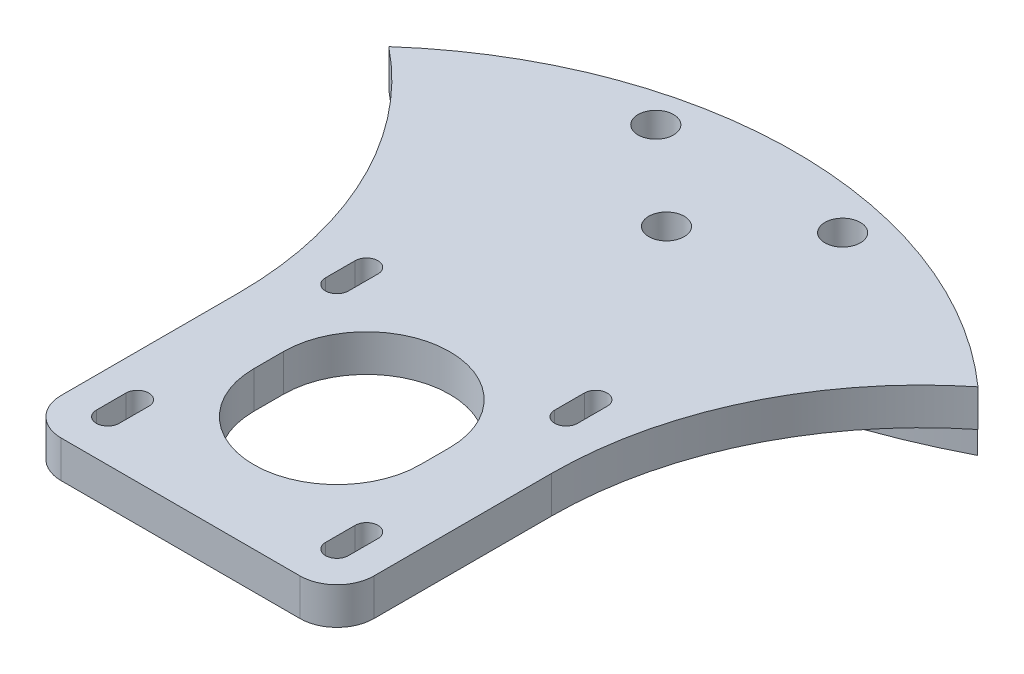
SolidWorks part; units mm, degrees
ref_plane "Front Plane" through (0, 0, 0) normal (0, 0, 1) x (1, 0, 0)
ref_plane "Top Plane" through (0, 0, 0) normal (0, 1, 0) x (1, 0, 0)
ref_plane "Right Plane" through (0, 0, 0) normal (1, 0, 0) x (0, 0, -1)
sketch "Sketch1" plane through (0, 0, 0) normal (0, 1, 0) x (1, 0, 0)
  circle A0 centre (0, 0) radius 72.63
  dimension "D1" = 145.26
extrude "Boss-Extrude1" add sketch "Sketch1" along normal blind 13
sketch "Sketch2" plane through (0, 13, 0) normal (0, 1, 0) x (1, 0, 0)
  line L2 (-21.15, -69.4823) -> (-21.15, -144.4823)
  line L3 (-21.15, -144.4823) -> (21.15, -144.4823)
  line L4 (21.15, -69.4823) -> (21.15, -144.4823)
  circle A1 centre (0, 0) radius 72.63
  arc A2 (21.15, -69.4823) -> (-21.15, -69.4823) centre (0, 0) ccw
  dimension "D2" = 42.3
  dimension "D3" = 75
  dimension "D1" = 0
extrude "Boss-Extrude2" add sketch "Sketch2" along normal blind 5
sketch "Sketch3" plane through (0, 0, 0) normal (0, -1, 0) x (1, 0, 0)
  circle A0 centre (0, 0) radius 101.6
  dimension "D1" = 203.2
sketch "Sketch4" plane through (0, 13, 0) normal (0, -1, 0) x (1, 0, 0)
  circle A0 centre (0, 0) radius 85.63
  arc A1 (21.15, 69.4823) -> (-21.15, 69.4823) centre (0, 0) ccw construction
  dimension "D1" = 13
extrude "Boss-Extrude3" add sketch "Sketch4" along normal blind 3.5 and the other way up to surface (5 mm away) other way up to face at (0, 18, 71.4542)
sketch "Sketch5" plane through (0, 13, 0) normal (0, -1, 0) x (1, 0, 0)
  line L0 (0, 123.3323) -> (0, 144.4823) construction
  line L1 (15.5, 107.8323) -> (-15.5, 107.8323) construction
  line L2 (15.5, 107.8323) -> (15.5, 138.8323) construction
  line L3 (15.5, 138.8323) -> (-15.5, 138.8323) construction
  line L4 (-15.5, 107.8323) -> (-15.5, 138.8323) construction
  line L5 (15.5, 107.8323) -> (-15.5, 138.8323) construction
  line L6 (15.5, 138.8323) -> (-15.5, 107.8323) construction
  line L7 (-21.15, 144.4823) -> (21.15, 144.4823) construction
  line L8 (0, 123.3323) -> (0, 119.3323) construction
  line L9 (11.25, 123.3323) -> (11.25, 119.3323)
  line L10 (-11.25, 123.3323) -> (-11.25, 119.3323)
  line L11 (15.5, 107.8323) -> (15.5, 103.8323) construction
  line L12 (17.05, 107.8323) -> (17.05, 103.8323)
  line L13 (13.95, 107.8323) -> (13.95, 103.8323)
  line L14 (15.5, 138.8323) -> (15.5, 134.8323) construction
  line L15 (17.05, 138.8323) -> (17.05, 134.8323)
  line L16 (13.95, 138.8323) -> (13.95, 134.8323)
  line L17 (-15.5, 138.8323) -> (-15.5, 134.8323) construction
  line L18 (-13.95, 138.8323) -> (-13.95, 134.8323)
  line L19 (-17.05, 138.8323) -> (-17.05, 134.8323)
  line L20 (-15.5, 107.8323) -> (-15.5, 103.8323) construction
  line L21 (-13.95, 107.8323) -> (-13.95, 103.8323)
  line L22 (-17.05, 107.8323) -> (-17.05, 103.8323)
  arc A0 (11.25, 123.3323) -> (-11.25, 123.3323) centre (0, 123.3323) ccw
  arc A1 (-11.25, 119.3323) -> (11.25, 119.3323) centre (0, 119.3323) ccw
  arc A2 (17.05, 107.8323) -> (13.95, 107.8323) centre (15.5, 107.8323) ccw
  arc A3 (13.95, 103.8323) -> (17.05, 103.8323) centre (15.5, 103.8323) ccw
  arc A4 (17.05, 138.8323) -> (13.95, 138.8323) centre (15.5, 138.8323) ccw
  arc A5 (13.95, 134.8323) -> (17.05, 134.8323) centre (15.5, 134.8323) ccw
  arc A6 (-13.95, 138.8323) -> (-17.05, 138.8323) centre (-15.5, 138.8323) ccw
  arc A7 (-17.05, 134.8323) -> (-13.95, 134.8323) centre (-15.5, 134.8323) ccw
  arc A8 (-13.95, 107.8323) -> (-17.05, 107.8323) centre (-15.5, 107.8323) ccw
  arc A9 (-17.05, 103.8323) -> (-13.95, 103.8323) centre (-15.5, 103.8323) ccw
  point P0 (0, 123.3323)
  point P9 (0, 121.3323)
  point P16 (15.5, 105.8323)
  point P22 (15.5, 136.8323)
  point P28 (-15.5, 136.8323)
  point P34 (-15.5, 105.8323)
  dimension "D1" = 21.15
  dimension "D2" = 31
  dimension "D3" = 4
  dimension "D4" = 22.5
  dimension "D5" = 3.1
  dimension "D6" = 4
  dimension "D7" = 4
  dimension "D8" = 3.1
extrude "Cut-Extrude1" cut sketch "Sketch5" against normal through all
fillet "Fillet1" radius 50 2 edges at (21.15, 15.5, 82.977) (-21.15, 15.5, 82.977)
fillet "Fillet2" radius 5 2 edges at (-21.15, 15.5, 144.4823) (21.15, 15.5, 144.4823)
sketch "Sketch7" plane through (0, 0, 0) normal (0, -1, 0) x (1, 0, 0)
  line L0 (11.25, 119.3323) -> (11.25, 123.3323) construction
  line L1 (-11.25, 123.3323) -> (-11.25, 119.3323) construction
  line L2 (11.25, 119.3323) -> (11.25, 123.3323) construction
  line L3 (-11.25, 123.3323) -> (-11.25, 119.3323) construction
  line L4 (-11.25, 121.3323) -> (11.25, 121.3323) construction
  line L5 (-62.6325, 80.8855) -> (-3.8977, 126.3659)
  line L6 (62.6325, 80.8855) -> (3.8977, 126.3659)
  circle A0 centre (0, 121.3323) radius 6.3662
  arc A1 (3.8977, 126.3659) -> (-3.8977, 126.3659) centre (0, 121.3323) ccw
  arc A2 (62.6325, 80.8855) -> (-62.6325, 80.8855) centre (0, 0) cw
  circle A4 centre (0, 0) radius 101.6 construction
  dimension "D1" = 12.7324
  dimension "D2" = 0.7
sketch "Sketch8" plane through (0, 9.5, 0) normal (0, -1, 0) x (1, 0, 0)
  line L0 (0, 72.63) -> (0, 85.63) construction
  circle A0 centre (0, 0) radius 72.63 construction
  circle A1 centre (0, 0) radius 85.63 construction
  circle A2 centre (0, 78.7622) radius 2.4
  dimension "D1" = 4.8
  dimension "D2" = 6.1322
extrude "Cut-Extrude2" cut sketch "Sketch8" against normal through all
sketch "Sketch10" plane through (0, 0, 0) normal (0, -1, 0) x (1, 0, 0)
  circle A0 centre (0, 121.3323) radius 60
  dimension "D1" = 120
extrude "Cut-Extrude3" cut sketch "Sketch10" against normal through all flip side to cut
sketch "Sketch11" plane through (0, 0, 0) normal (0, -1, 0) x (1, 0, 0)
  line L0 (-26.6369, 67.5692) -> (26.6369, 67.5692) construction
  circle A0 centre (-12.6369, 67.5692) radius 2.4
  circle A1 centre (12.6369, 67.5692) radius 2.4
  dimension "D1" = 4.8
  dimension "D2" = 14
  dimension "D3" = 14
extrude "Cut-Extrude4" cut sketch "Sketch11" against normal through all
